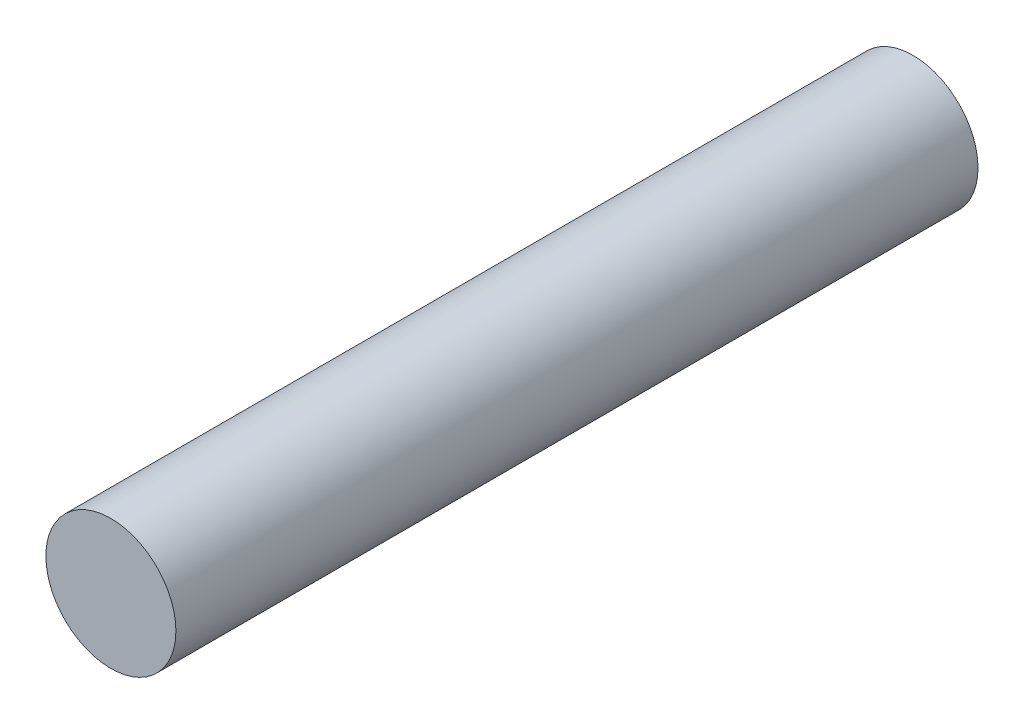
SolidWorks part; units mm, degrees
ref_plane "Front Plane" through (0, 0, 0) normal (0, 0, 1) x (1, 0, 0)
ref_plane "Top Plane" through (0, 0, 0) normal (0, 1, 0) x (1, 0, 0)
ref_plane "Right Plane" through (0, 0, 0) normal (1, 0, 0) x (0, 0, -1)
sketch "Sketch1" plane through (0, 0, 0) normal (0, 0, 1) x (1, 0, 0)
  circle A0 centre (0, 0) radius 0.65
  dimension "D1" = 1.3
extrude "Extrude1" add sketch "Sketch1" along normal blind 8.02
